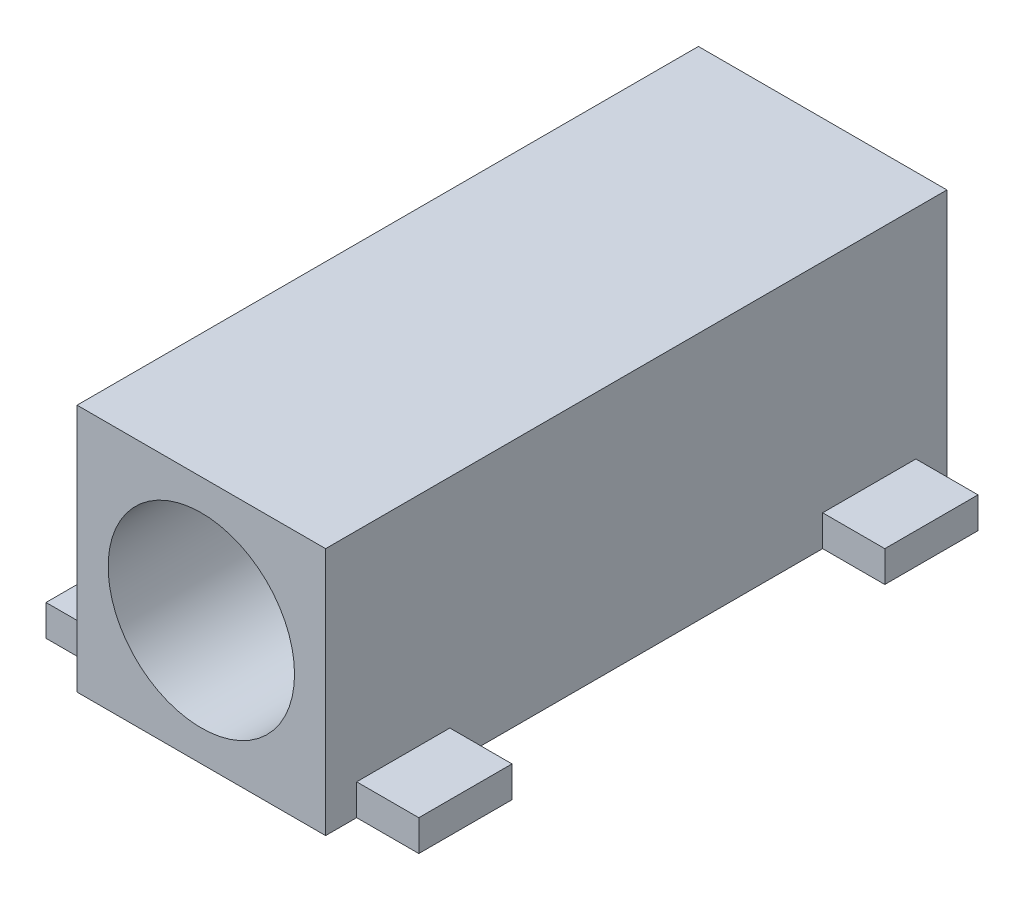
SolidWorks part; units mm, degrees
ref_plane "Front Plane" through (0, 0, 0) normal (0, 0, 1) x (1, 0, 0)
ref_plane "Top Plane" through (0, 0, 0) normal (0, 1, 0) x (1, 0, 0)
ref_plane "Right Plane" through (0, 0, 0) normal (1, 0, 0) x (0, 0, -1)
sketch "Sketch1" plane through (0, 0, 0) normal (0, 0, 1) x (1, 0, 0)
  line L1 (-2, 2) -> (2, 2)
  line L2 (-2, 2) -> (-2, -2)
  line L3 (-2, -2) -> (2, -2)
  line L4 (2, 2) -> (2, -2)
  circle A0 centre (0, 0) radius 1.5
  point P7 (0, 2)
  point P8 (2, 0)
  dimension "D2" = 3
  dimension "D1" = 4
extrude "Boss-Extrude1" add sketch "Sketch1" along normal blind 10
sketch "Sketch3" plane through (2, 0, 0) normal (1, 0, 0) x (0, 0, -1)
  line L0 (-10, -2) -> (0, -2) construction
  line L1 (-9.5, -2) -> (-8, -2)
  line L2 (-9.5, -2) -> (-9.5, -1.5)
  line L3 (-9.5, -1.5) -> (-8, -1.5)
  line L4 (-8, -2) -> (-8, -1.5)
  line L5 (-10, -2) -> (-10, 2) construction
  line L6 (-2, -2) -> (-0.5, -2)
  line L7 (-2, -2) -> (-2, -1.5)
  line L8 (-2, -1.5) -> (-0.5, -1.5)
  line L9 (-0.5, -2) -> (-0.5, -1.5)
  line L10 (0, -2) -> (0, 2) construction
  dimension "D1" = 1.5
  dimension "D2" = 0.5
  dimension "D3" = 0.5
  dimension "D4" = 0.5
extrude "Boss-Extrude2" add sketch "Sketch3" along normal blind 1
sketch "Sketch4" plane through (-2, 0, 0) normal (-1, 0, 0) x (0, 0, 1)
  line L0 (10, -2) -> (0, -2) construction
  line L1 (9.5, -2) -> (8, -2)
  line L2 (9.5, -2) -> (9.5, -1.5)
  line L3 (9.5, -1.5) -> (8, -1.5)
  line L4 (8, -2) -> (8, -1.5)
  line L5 (10, 2) -> (10, -2) construction
  dimension "D1" = 1.5
  dimension "D2" = 0.5
  dimension "D3" = 0.5
extrude "Boss-Extrude3" add sketch "Sketch4" along normal blind 1
